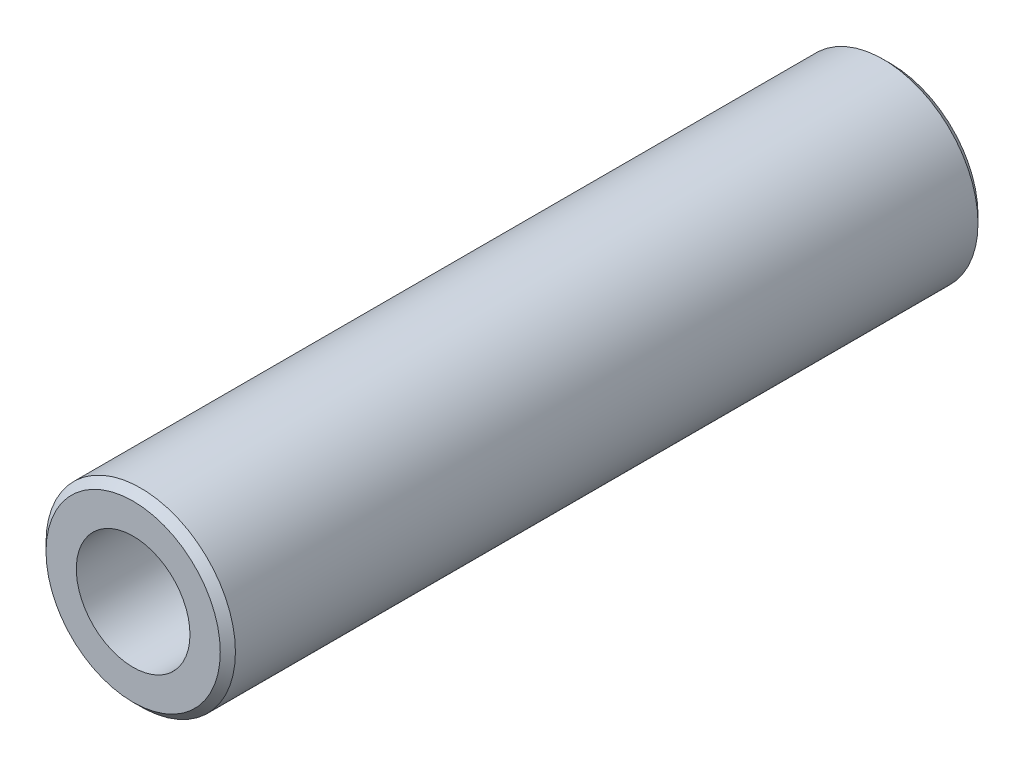
SolidWorks part; units mm, degrees
ref_plane "Front Plane" through (0, 0, 0) normal (0, 0, 1) x (1, 0, 0)
ref_plane "Top Plane" through (0, 0, 0) normal (0, 1, 0) x (1, 0, 0)
ref_plane "Right Plane" through (0, 0, 0) normal (1, 0, 0) x (0, 0, -1)
sketch "Sketch1" plane through (0, 0, 0) normal (0, 0, 1) x (1, 0, 0)
  circle A0 centre (0, 0) radius 6.25
  dimension "D1" = 12.5
extrude "Extrude-Thin1" add sketch "Sketch1" along normal mid plane 50 thin thin type one direction reverse wall 2.5
chamfer "Chamfer1" distance 0.5 angle 45 2 edges at (6.25, 0, -25) (6.25, 0, 25)
